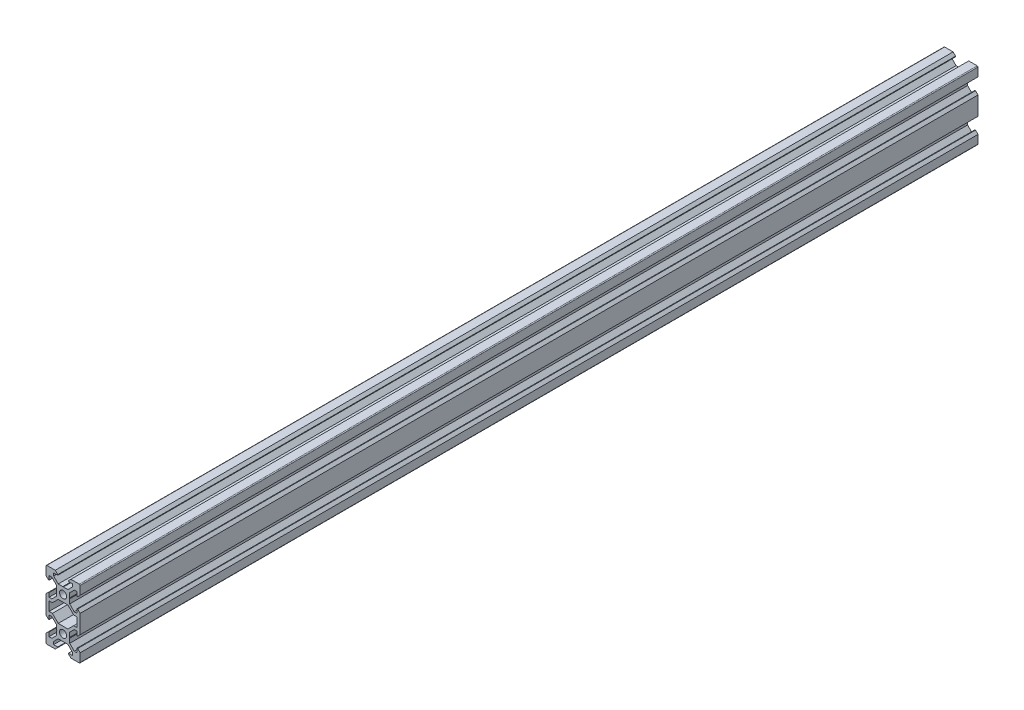
SolidWorks part; units mm, degrees
material "6061-T6 (SS)"
ref_plane "Front Plane" through (0, 0, 0) normal (0, 0, 1) x (1, 0, 0)
ref_plane "Top Plane" through (0, 0, 0) normal (0, 1, 0) x (1, 0, 0)
ref_plane "Right Plane" through (0, 0, 0) normal (1, 0, 0) x (0, 0, -1)
sketch "Sketch1" plane through (0, 0, 0) normal (0, 0, 1) x (1, 0, 0)
  line L0 (0, 0) -> (10, 0) construction
  line L1 (9.5, -20) -> (-9.5, -20)
  line L2 (10, -19.5) -> (10, 19.5)
  line L3 (9.5, 20) -> (-9.5, 20)
  line L4 (-10, -19.5) -> (-10, 19.5)
  line L5 (10, -20) -> (-10, 20) construction
  line L6 (10, 20) -> (-10, -20) construction
  circle A0 centre (0, 10) radius 2.1
  circle A1 centre (0, -10) radius 2.1
  arc A2 (-9.5, -20) -> (-10, -19.5) centre (-9.5, -19.5) cw
  arc A3 (9.5, -20) -> (10, -19.5) centre (9.5, -19.5) ccw
  arc A4 (10, 19.5) -> (9.5, 20) centre (9.5, 19.5) ccw
  arc A5 (-9.5, 20) -> (-10, 19.5) centre (-9.5, 19.5) ccw
  point P0 (0, 0)
  line B0 (0, 10) -> (0, 20) construction
  line B1 (0, 13.69) -> (-0.21, 13.9)
  line B2 (-0.21, 13.9) -> (-2.8393, 13.9)
  line B3 (-2.8393, 13.9) -> (-5.5, 16.5607)
  line B4 (-5.5, 16.5607) -> (-5.5, 18.2)
  line B5 (-5.5, 18.2) -> (-3.125, 18.2)
  line B6 (-3.125, 18.2) -> (-3.125, 18.545)
  line B7 (-3.125, 18.545) -> (-4.58, 20)
  line B8 (-4.58, 20) -> (4.58, 20)
  line B9 (0, 10) -> (-5.9132, 15.9132) construction
  line B10 (3.125, 18.545) -> (4.58, 20)
  line B11 (3.125, 18.2) -> (3.125, 18.545)
  line B12 (5.5, 18.2) -> (3.125, 18.2)
  line B13 (5.5, 16.5607) -> (5.5, 18.2)
  line B14 (2.8393, 13.9) -> (5.5, 16.5607)
  line B15 (0.21, 13.9) -> (2.8393, 13.9)
  line B16 (0, 13.69) -> (0.21, 13.9)
  line B17 (0, 10) -> (-10, 10) construction
  line B18 (-3.69, 10) -> (-3.9, 9.79)
  line B19 (-3.9, 9.79) -> (-3.9, 7.1607)
  line B20 (-3.9, 7.1607) -> (-6.5607, 4.5)
  line B21 (-6.5607, 4.5) -> (-8.2, 4.5)
  line B22 (-8.2, 4.5) -> (-8.2, 6.875)
  line B23 (-8.2, 6.875) -> (-8.545, 6.875)
  line B24 (-8.545, 6.875) -> (-10, 5.42)
  line B25 (-10, 5.42) -> (-10, 14.58)
  line B26 (0, 10) -> (-5.9132, 4.0868) construction
  line B27 (-8.545, 13.125) -> (-10, 14.58)
  line B28 (-8.2, 13.125) -> (-8.545, 13.125)
  line B29 (-8.2, 15.5) -> (-8.2, 13.125)
  line B30 (-6.5607, 15.5) -> (-8.2, 15.5)
  line B31 (-3.9, 12.8393) -> (-6.5607, 15.5)
  line B32 (-3.9, 10.21) -> (-3.9, 12.8393)
  line B33 (-3.69, 10) -> (-3.9, 10.21)
  line B34 (0, -10) -> (-10, -10) construction
  line B35 (-3.69, -10) -> (-3.9, -10.21)
  line B36 (-3.9, -10.21) -> (-3.9, -12.8393)
  line B37 (-3.9, -12.8393) -> (-6.5607, -15.5)
  line B38 (-6.5607, -15.5) -> (-8.2, -15.5)
  line B39 (-8.2, -15.5) -> (-8.2, -13.125)
  line B40 (-8.2, -13.125) -> (-8.545, -13.125)
  line B41 (-8.545, -13.125) -> (-10, -14.58)
  line B42 (-10, -14.58) -> (-10, -5.42)
  line B43 (0, -10) -> (-5.9132, -15.9132) construction
  line B44 (-8.545, -6.875) -> (-10, -5.42)
  line B45 (-8.2, -6.875) -> (-8.545, -6.875)
  line B46 (-8.2, -4.5) -> (-8.2, -6.875)
  line B47 (-6.5607, -4.5) -> (-8.2, -4.5)
  line B48 (-3.9, -7.1607) -> (-6.5607, -4.5)
  line B49 (-3.9, -9.79) -> (-3.9, -7.1607)
  line B50 (-3.69, -10) -> (-3.9, -9.79)
  line B51 (0, -10) -> (0, -20) construction
  line B52 (0, -13.69) -> (0.21, -13.9)
  line B53 (0.21, -13.9) -> (2.8393, -13.9)
  line B54 (2.8393, -13.9) -> (5.5, -16.5607)
  line B55 (5.5, -16.5607) -> (5.5, -18.2)
  line B56 (5.5, -18.2) -> (3.125, -18.2)
  line B57 (3.125, -18.2) -> (3.125, -18.545)
  line B58 (3.125, -18.545) -> (4.58, -20)
  line B59 (4.58, -20) -> (-4.58, -20)
  line B60 (0, -10) -> (5.9132, -15.9132) construction
  line B61 (-3.125, -18.545) -> (-4.58, -20)
  line B62 (-3.125, -18.2) -> (-3.125, -18.545)
  line B63 (-5.5, -18.2) -> (-3.125, -18.2)
  line B64 (-5.5, -16.5607) -> (-5.5, -18.2)
  line B65 (-2.8393, -13.9) -> (-5.5, -16.5607)
  line B66 (-0.21, -13.9) -> (-2.8393, -13.9)
  line B67 (0, -13.69) -> (-0.21, -13.9)
  line B68 (0, -10) -> (10, -10) construction
  line B69 (3.69, -10) -> (3.9, -9.79)
  line B70 (3.9, -9.79) -> (3.9, -7.1607)
  line B71 (3.9, -7.1607) -> (6.5607, -4.5)
  line B72 (6.5607, -4.5) -> (8.2, -4.5)
  line B73 (8.2, -4.5) -> (8.2, -6.875)
  line B74 (8.2, -6.875) -> (8.545, -6.875)
  line B75 (8.545, -6.875) -> (10, -5.42)
  line B76 (10, -5.42) -> (10, -14.58)
  line B77 (0, -10) -> (5.9132, -4.0868) construction
  line B78 (8.545, -13.125) -> (10, -14.58)
  line B79 (8.2, -13.125) -> (8.545, -13.125)
  line B80 (8.2, -15.5) -> (8.2, -13.125)
  line B81 (6.5607, -15.5) -> (8.2, -15.5)
  line B82 (3.9, -12.8393) -> (6.5607, -15.5)
  line B83 (3.9, -10.21) -> (3.9, -12.8393)
  line B84 (3.69, -10) -> (3.9, -10.21)
  line B85 (0, 10) -> (10, 10) construction
  line B86 (3.69, 10) -> (3.9, 10.21)
  line B87 (3.9, 10.21) -> (3.9, 12.8393)
  line B88 (3.9, 12.8393) -> (6.5607, 15.5)
  line B89 (6.5607, 15.5) -> (8.2, 15.5)
  line B90 (8.2, 15.5) -> (8.2, 13.125)
  line B91 (8.2, 13.125) -> (8.545, 13.125)
  line B92 (8.545, 13.125) -> (10, 14.58)
  line B93 (10, 14.58) -> (10, 5.42)
  line B94 (0, 10) -> (5.9132, 15.9132) construction
  line B95 (8.545, 6.875) -> (10, 5.42)
  line B96 (8.2, 6.875) -> (8.545, 6.875)
  line B97 (8.2, 4.5) -> (8.2, 6.875)
  line B98 (6.5607, 4.5) -> (8.2, 4.5)
  line B99 (3.9, 7.1607) -> (6.5607, 4.5)
  line B100 (3.9, 9.79) -> (3.9, 7.1607)
  line B101 (3.69, 10) -> (3.9, 9.79)
  line B102 (-8.2, -2.7) -> (-8.2, 2.7)
  line B103 (-8.2, 2.7) -> (-6.2393, 2.7)
  line B104 (-6.2393, 2.7) -> (-2.8393, 6.1)
  line B105 (-2.8393, 6.1) -> (2.8393, 6.1)
  line B106 (0, 6.1) -> (0, 0) construction
  line B107 (0, 0) -> (-8.2, 0) construction
  line B108 (6.2393, 2.7) -> (2.8393, 6.1)
  line B109 (8.2, 2.7) -> (6.2393, 2.7)
  line B110 (8.2, -2.7) -> (8.2, 2.7)
  line B111 (8.2, -2.7) -> (6.2393, -2.7)
  line B112 (6.2393, -2.7) -> (2.8393, -6.1)
  line B113 (-2.8393, -6.1) -> (2.8393, -6.1)
  line B114 (-6.2393, -2.7) -> (-2.8393, -6.1)
  line B115 (-8.2, -2.7) -> (-6.2393, -2.7)
  line B116 (0, 6.1) -> (0, 10) construction
  line B117 (0, 10) -> (-5.0927, 4.9073) construction
  dimension "D4" = 4.2
  dimension "D5" = 0.5
  dimension "D1" = 20
  dimension "D2" = 40
  dimension "D3" = 20
sketch_block_instance "V Slot 1-4"
sketch_block "V Slot 1" parameters "D1"=10, "D2"=11, "D3"=4.3, "D4"=1.8, "D5"=0.21, "D6"=45, "D7"=9.16, "D8"=1.5, "D9"=6.25
sketch_block_instance "V Slot 1-5"
sketch_block_instance "V Slot 1-6"
sketch_block_instance "V Slot 1-7"
sketch_block_instance "V Slot 1-8"
sketch_block_instance "V Slot 1-9"
sketch_block_instance "Center Cutout 1-1"
sketch_block "Center Cutout 1" parameters "D1"=5.4, "D2"=12.2, "D3"=8.2, "D4"=45, "D5"=10, "D6"=1.5
extrude "Boss-Extrude1" add sketch "Sketch1" along normal blind 526 contours B101 B86 B87 B88 B89 B90 B91 B92 L2 A4 L3 B10 B11 B12 B13 B14 B15 B16 B1 B2 B3 B4 B5 B6 B7 A5 L4 B27 B28 B29 B30 B31 B32 B33 B18 B19 B20 B21 B22 B23 B24 B44 B45 B46 B47 B48 B49 B50 B35
